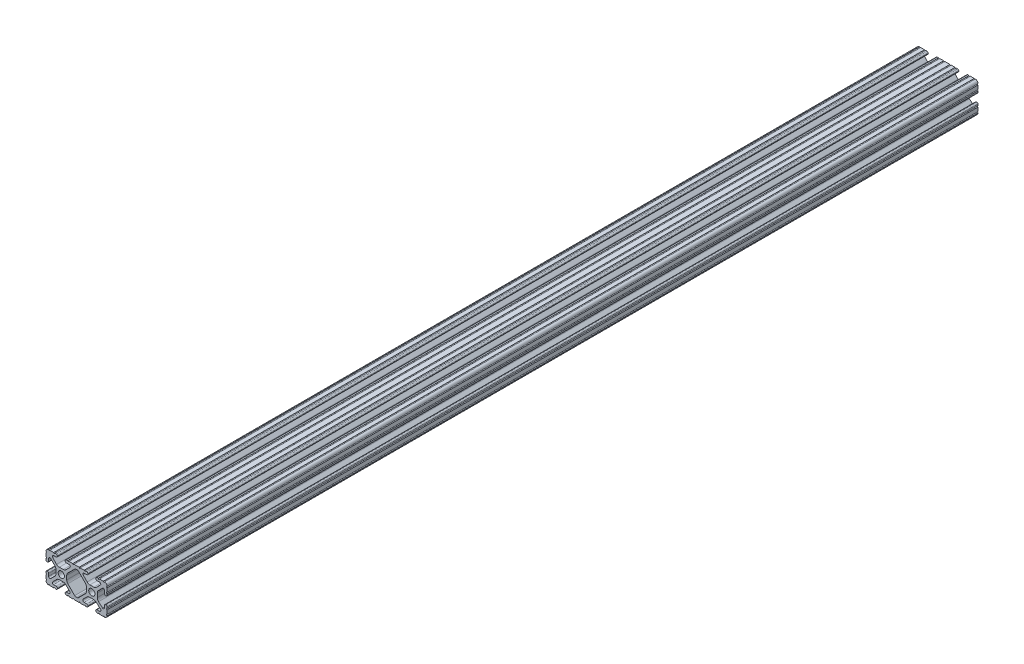
SolidWorks part; units mm, degrees
ref_plane "Front Plane" through (0, 0, 0) normal (0, 0, 1) x (1, 0, 0)
ref_plane "Top Plane" through (0, 0, 0) normal (0, 1, 0) x (1, 0, 0)
ref_plane "Right Plane" through (0, 0, 0) normal (1, 0, 0) x (0, 0, -1)
sketch "Sketch1" plane through (0, 0, 0) normal (0, 0, 1) x (1, 0, 0)
  line L0 (-7.2595, -3.8694) -> (-1.5457, -9.5728)
  line L1 (-8.1915, 1.6223) -> (-8.1915, -1.6223)
  line L2 (-1.504, 9.5765) -> (-7.252, 3.8768)
  line L3 (0.5515, 10.033) -> (-0.3952, 10.033)
  line L4 (7.2829, 3.8459) -> (1.6756, 9.5611)
  line L5 (8.1915, -1.6223) -> (8.1915, 1.6223)
  line L6 (1.5457, -9.5728) -> (7.2595, -3.8694)
  line L7 (-0.4332, -10.033) -> (0.4332, -10.033)
  line L8 (18.0171, 12.7) -> (16.9875, 12.7)
  line L9 (15.9385, 11.651) -> (15.9385, 11.5392)
  line L10 (16.9875, 10.4902) -> (19.1164, 10.4902)
  line L11 (19.8441, 8.7652) -> (16.619, 5.4551)
  line L12 (14.3449, 4.4958) -> (11.0833, 4.4958)
  line L13 (8.817, 5.4472) -> (5.5642, 8.7627)
  line L14 (6.2894, 10.4902) -> (8.4125, 10.4902)
  line L15 (9.4615, 11.5392) -> (9.4615, 11.651)
  line L16 (8.4125, 12.7) -> (7.3829, 12.7)
  line L17 (6.3669, 12.7) -> (3.1496, 12.7)
  line L18 (2.1336, 12.7) -> (-2.1336, 12.7)
  line L19 (-3.1496, 12.7) -> (-6.3669, 12.7)
  line L20 (-7.3829, 12.7) -> (-8.4125, 12.7)
  line L21 (-9.4615, 11.651) -> (-9.4615, 11.5392)
  line L22 (-8.4125, 10.4902) -> (-6.2836, 10.4902)
  line L23 (-5.5326, 8.6661) -> (-8.81, 5.4163)
  line L24 (-11.0455, 4.4958) -> (-14.3545, 4.4958)
  line L25 (-16.59, 5.4163) -> (-19.8674, 8.6661)
  line L26 (-19.1164, 10.4902) -> (-16.9875, 10.4902)
  line L27 (-15.9385, 11.5392) -> (-15.9385, 11.651)
  line L28 (-16.9875, 12.7) -> (-18.0171, 12.7)
  line L29 (-19.0331, 12.7) -> (-22.2504, 12.7)
  line L30 (-25.4, 9.5504) -> (-25.4, 6.3331)
  line L31 (-25.4, 5.3171) -> (-25.4, 4.2375)
  line L32 (-24.401, 3.2385) -> (-24.2392, 3.2385)
  line L33 (-23.1902, 4.2875) -> (-23.1902, 6.3347)
  line L34 (-21.434, 7.0665) -> (-18.148, 3.8082)
  line L35 (-17.2085, 1.5536) -> (-17.2085, -1.6952)
  line L36 (-18.1405, -3.9423) -> (-21.4316, -7.2274)
  line L37 (-23.1902, -6.498) -> (-23.1902, -4.2875)
  line L38 (-24.2392, -3.2385) -> (-24.351, -3.2385)
  line L39 (-25.4, -4.2875) -> (-25.4, -5.3171)
  line L40 (-25.4, -6.3331) -> (-25.4, -9.5504)
  line L41 (-22.2504, -12.7) -> (-19.0331, -12.7)
  line L42 (-18.0171, -12.7) -> (-16.9875, -12.7)
  line L43 (-15.9384, -11.651) -> (-15.9384, -11.5392)
  line L44 (-16.9875, -10.4902) -> (-19.1164, -10.4902)
  line L45 (-19.8341, -8.7551) -> (-16.4966, -5.4237)
  line L46 (-14.2536, -4.4958) -> (-11.1464, -4.4958)
  line L47 (-8.9034, -5.4237) -> (-5.5659, -8.7551)
  line L48 (-6.2836, -10.4902) -> (-8.4125, -10.4902)
  line L49 (-9.4616, -11.5392) -> (-9.4616, -11.651)
  line L50 (-8.4125, -12.7) -> (-7.3829, -12.7)
  line L51 (-6.3669, -12.7) -> (-3.1496, -12.7)
  line L52 (-2.1336, -12.7) -> (2.1336, -12.7)
  line L53 (3.1496, -12.7) -> (6.3669, -12.7)
  line L54 (7.3829, -12.7) -> (8.4125, -12.7)
  line L55 (9.4616, -11.651) -> (9.4616, -11.5392)
  line L56 (8.4125, -10.4902) -> (6.2894, -10.4902)
  line L57 (5.4807, -8.5353) -> (8.5979, -5.4237)
  line L58 (10.8409, -4.4958) -> (14.1026, -4.4958)
  line L59 (16.1879, -5.2766) -> (19.8682, -8.4822)
  line L60 (19.1164, -10.4902) -> (16.9875, -10.4902)
  line L61 (15.9384, -11.5392) -> (15.9384, -11.651)
  line L62 (16.9875, -12.7) -> (18.0171, -12.7)
  line L63 (19.0331, -12.7) -> (22.2504, -12.7)
  line L64 (25.4, -9.5504) -> (25.4, -6.3331)
  line L65 (25.4, -5.3171) -> (25.4, -4.2375)
  line L66 (24.401, -3.2385) -> (24.1892, -3.2385)
  line L67 (23.1902, -4.2375) -> (23.1902, -6.1559)
  line L68 (21.584, -6.8869) -> (18.2982, -4.025)
  line L69 (17.2085, -1.6308) -> (17.2085, 1.6308)
  line L70 (18.1094, 3.8465) -> (21.5263, 7.3534)
  line L71 (23.1902, 6.6769) -> (23.1902, 4.2375)
  line L72 (24.1892, 3.2385) -> (24.401, 3.2385)
  line L73 (25.4, 4.2375) -> (25.4, 5.3171)
  line L74 (25.4, 6.3332) -> (25.4, 9.5504)
  line L75 (22.2504, 12.7) -> (19.0331, 12.7)
  circle A0 centre (-12.7, 0) radius 2.6035
  circle A1 centre (12.7, 0) radius 2.6035
  arc A2 (-1.5457, -9.5728) -> (-0.4332, -10.033) centre (-0.4332, -8.4582) ccw
  arc A3 (-8.1915, -1.6223) -> (-7.2595, -3.8694) centre (-5.0165, -1.6223) ccw
  arc A4 (-7.252, 3.8768) -> (-8.1915, 1.6223) centre (-5.0165, 1.6223) ccw
  arc A5 (-0.3952, 10.033) -> (-1.504, 9.5765) centre (-0.3952, 8.4582) ccw
  arc A6 (1.6756, 9.5611) -> (0.5515, 10.033) centre (0.5515, 8.4582) ccw
  arc A7 (8.1915, 1.6223) -> (7.2829, 3.8459) centre (5.0165, 1.6223) ccw
  arc A8 (7.2595, -3.8694) -> (8.1915, -1.6223) centre (5.0165, -1.6223) ccw
  arc A9 (0.4332, -10.033) -> (1.5457, -9.5728) centre (0.4332, -8.4582) ccw
  arc A10 (18.0171, 12.7) -> (19.0331, 12.7) centre (18.5251, 12.7) ccw
  arc A11 (16.9875, 12.7) -> (15.9385, 11.651) centre (16.9875, 11.651) ccw
  arc A12 (15.9385, 11.5392) -> (16.9875, 10.4902) centre (16.9875, 11.5392) ccw
  arc A13 (19.8441, 8.7652) -> (19.1164, 10.4902) centre (19.1164, 9.4742) ccw
  arc A14 (14.3449, 4.4958) -> (16.619, 5.4551) centre (14.3449, 7.6708) ccw
  arc A15 (8.817, 5.4472) -> (11.0833, 4.4958) centre (11.0833, 7.6708) ccw
  arc A16 (6.2894, 10.4902) -> (5.5642, 8.7627) centre (6.2894, 9.4742) ccw
  arc A17 (8.4125, 10.4902) -> (9.4615, 11.5392) centre (8.4125, 11.5392) ccw
  arc A18 (9.4615, 11.651) -> (8.4125, 12.7) centre (8.4125, 11.651) ccw
  arc A19 (6.3669, 12.7) -> (7.3829, 12.7) centre (6.8749, 12.7) ccw
  arc A20 (2.1336, 12.7) -> (3.1496, 12.7) centre (2.6416, 12.7) ccw
  arc A21 (-3.1496, 12.7) -> (-2.1336, 12.7) centre (-2.6416, 12.7) ccw
  arc A22 (-7.3829, 12.7) -> (-6.3669, 12.7) centre (-6.8749, 12.7) ccw
  arc A23 (-8.4125, 12.7) -> (-9.4615, 11.651) centre (-8.4125, 11.651) ccw
  arc A24 (-9.4615, 11.5392) -> (-8.4125, 10.4902) centre (-8.4125, 11.5392) ccw
  arc A25 (-5.5326, 8.6661) -> (-6.2836, 10.4902) centre (-6.2836, 9.4235) ccw
  arc A26 (-11.0455, 4.4958) -> (-8.81, 5.4163) centre (-11.0455, 7.6708) ccw
  arc A27 (-16.59, 5.4163) -> (-14.3545, 4.4958) centre (-14.3545, 7.6708) ccw
  arc A28 (-19.1164, 10.4902) -> (-19.8674, 8.6661) centre (-19.1164, 9.4235) ccw
  arc A29 (-16.9875, 10.4902) -> (-15.9385, 11.5392) centre (-16.9875, 11.5392) ccw
  arc A30 (-15.9385, 11.651) -> (-16.9875, 12.7) centre (-16.9875, 11.651) ccw
  arc A31 (-19.0331, 12.7) -> (-18.0171, 12.7) centre (-18.5251, 12.7) ccw
  arc A32 (-23.2664, 12.6998) -> (-22.2504, 12.7) centre (-22.7584, 12.7) ccw
  arc A33 (-23.2664, 12.6998) -> (-25.3998, 10.5664) centre (-23.2918, 10.5918) ccw
  arc A34 (-25.4, 9.5504) -> (-25.3998, 10.5664) centre (-25.4, 10.0584) ccw
  arc A35 (-25.4, 5.3171) -> (-25.4, 6.3331) centre (-25.4, 5.8251) ccw
  arc A36 (-25.4, 4.2375) -> (-24.401, 3.2385) centre (-24.401, 4.2375) ccw
  arc A37 (-24.2392, 3.2385) -> (-23.1902, 4.2875) centre (-24.2392, 4.2875) ccw
  arc A38 (-21.434, 7.0665) -> (-23.1902, 6.3347) centre (-22.1596, 6.3347) ccw
  arc A39 (-17.2085, 1.5536) -> (-18.148, 3.8082) centre (-20.3835, 1.5536) ccw
  arc A40 (-18.1405, -3.9423) -> (-17.2085, -1.6952) centre (-20.3835, -1.6952) ccw
  arc A41 (-23.1902, -6.498) -> (-21.4316, -7.2274) centre (-22.1596, -6.498) ccw
  arc A42 (-23.1902, -4.2875) -> (-24.2392, -3.2385) centre (-24.2392, -4.2875) ccw
  arc A43 (-24.351, -3.2385) -> (-25.4, -4.2875) centre (-24.351, -4.2875) ccw
  arc A44 (-25.4, -6.3331) -> (-25.4, -5.3171) centre (-25.4, -5.8251) ccw
  arc A45 (-25.3998, -10.5664) -> (-25.4, -9.5504) centre (-25.4, -10.0584) ccw
  arc A46 (-25.3998, -10.5664) -> (-23.2664, -12.6998) centre (-23.2918, -10.5918) ccw
  arc A47 (-22.2504, -12.7) -> (-23.2664, -12.6998) centre (-22.7584, -12.7) ccw
  arc A48 (-18.0171, -12.7) -> (-19.0331, -12.7) centre (-18.5251, -12.7) ccw
  arc A49 (-16.9875, -12.7) -> (-15.9384, -11.651) centre (-16.9875, -11.651) ccw
  arc A50 (-15.9384, -11.5392) -> (-16.9875, -10.4902) centre (-16.9875, -11.5392) ccw
  arc A51 (-19.8341, -8.7551) -> (-19.1164, -10.4902) centre (-19.1164, -9.4742) ccw
  arc A52 (-14.2536, -4.4958) -> (-16.4966, -5.4237) centre (-14.2536, -7.6708) ccw
  arc A53 (-8.9034, -5.4237) -> (-11.1464, -4.4958) centre (-11.1464, -7.6708) ccw
  arc A54 (-6.2836, -10.4902) -> (-5.5659, -8.7551) centre (-6.2836, -9.4742) ccw
  arc A55 (-8.4125, -10.4902) -> (-9.4616, -11.5392) centre (-8.4125, -11.5392) ccw
  arc A56 (-9.4616, -11.651) -> (-8.4125, -12.7) centre (-8.4125, -11.651) ccw
  arc A57 (-6.3669, -12.7) -> (-7.3829, -12.7) centre (-6.8749, -12.7) ccw
  arc A58 (-2.1336, -12.7) -> (-3.1496, -12.7) centre (-2.6416, -12.7) ccw
  arc A59 (3.1496, -12.7) -> (2.1336, -12.7) centre (2.6416, -12.7) ccw
  arc A60 (7.3829, -12.7) -> (6.3669, -12.7) centre (6.8749, -12.7) ccw
  arc A61 (8.4125, -12.7) -> (9.4616, -11.651) centre (8.4125, -11.651) ccw
  arc A62 (9.4616, -11.5392) -> (8.4125, -10.4902) centre (8.4125, -11.5392) ccw
  arc A63 (5.4807, -8.5353) -> (6.2894, -10.4902) centre (6.2894, -9.3455) ccw
  arc A64 (10.8409, -4.4958) -> (8.5979, -5.4237) centre (10.8409, -7.6708) ccw
  arc A65 (16.1879, -5.2766) -> (14.1026, -4.4958) centre (14.1026, -7.6708) ccw
  arc A66 (19.1164, -10.4902) -> (19.8682, -8.4822) centre (19.1164, -9.3455) ccw
  arc A67 (16.9875, -10.4902) -> (15.9384, -11.5392) centre (16.9875, -11.5392) ccw
  arc A68 (15.9384, -11.651) -> (16.9875, -12.7) centre (16.9875, -11.651) ccw
  arc A69 (19.0331, -12.7) -> (18.0171, -12.7) centre (18.5251, -12.7) ccw
  arc A70 (23.2664, -12.6998) -> (22.2504, -12.7) centre (22.7584, -12.7) ccw
  arc A71 (23.2664, -12.6998) -> (25.3998, -10.5664) centre (23.2918, -10.5918) ccw
  arc A72 (25.4, -9.5504) -> (25.3998, -10.5664) centre (25.4, -10.0584) ccw
  arc A73 (25.4, -5.3171) -> (25.4, -6.3331) centre (25.4, -5.8251) ccw
  arc A74 (25.4, -4.2375) -> (24.401, -3.2385) centre (24.401, -4.2375) ccw
  arc A75 (24.1892, -3.2385) -> (23.1902, -4.2375) centre (24.1892, -4.2375) ccw
  arc A76 (21.584, -6.8869) -> (23.1902, -6.1559) centre (22.2207, -6.1559) ccw
  arc A77 (17.2085, -1.6308) -> (18.2982, -4.025) centre (20.3835, -1.6308) ccw
  arc A78 (18.1094, 3.8465) -> (17.2085, 1.6308) centre (20.3835, 1.6308) ccw
  arc A79 (23.1902, 6.6769) -> (21.5263, 7.3534) centre (22.2207, 6.6769) ccw
  arc A80 (23.1902, 4.2375) -> (24.1892, 3.2385) centre (24.1892, 4.2375) ccw
  arc A81 (24.401, 3.2385) -> (25.4, 4.2375) centre (24.401, 4.2375) ccw
  arc A82 (25.4, 6.3332) -> (25.4, 5.3171) centre (25.4, 5.8251) ccw
  arc A83 (25.3998, 10.5664) -> (25.4, 9.5504) centre (25.4, 10.0584) ccw
  arc A84 (25.3998, 10.5664) -> (23.2664, 12.6998) centre (23.2918, 10.5918) ccw
  arc A85 (22.2504, 12.7) -> (23.2664, 12.6998) centre (22.7584, 12.7) ccw
  point P248 (0, 10.033)
extrude "Boss-Extrude1" add sketch "Sketch1" along normal mid plane 723.9
